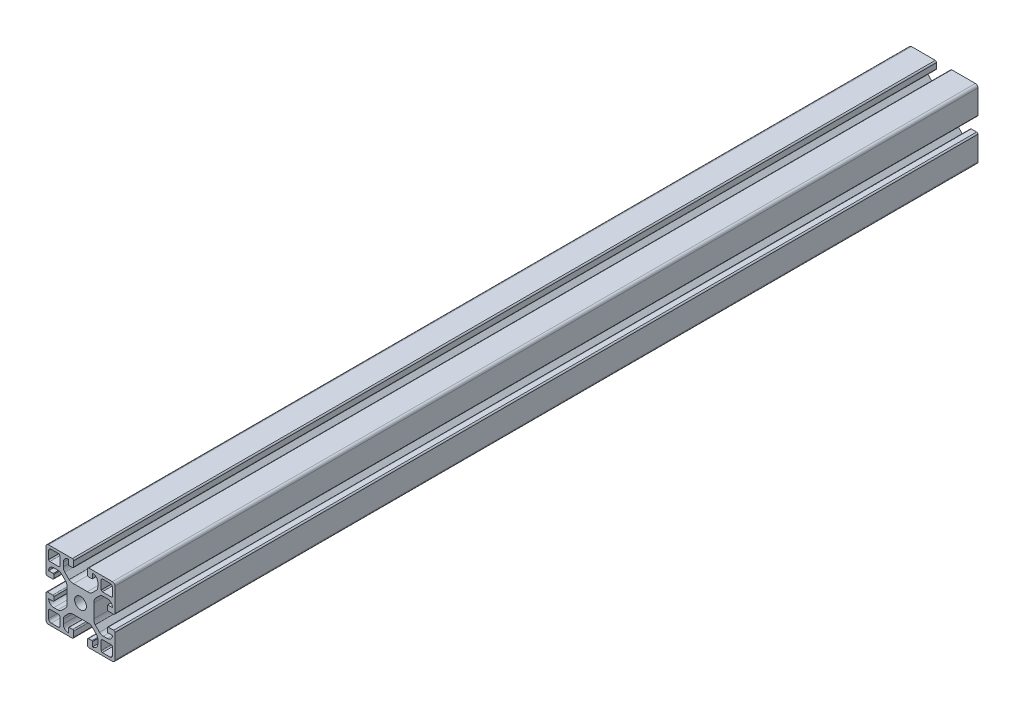
SolidWorks part; units mm, degrees
ref_plane "Alzado" through (0, 0, 0) normal (0, 0, 1) x (1, 0, 0)
ref_plane "Planta" through (0, 0, 0) normal (0, 1, 0) x (1, 0, 0)
ref_plane "Vista lateral" through (0, 0, 0) normal (1, 0, 0) x (0, 0, -1)
sketch "Croquis1" plane through (0, 0, 0) normal (0, 0, 1) x (1, 0, 0)
  line L9 (0, 18.5) -> (0, 4.7232)
  line L10 (0.7765, 4) -> (3.8765, 4)
  line L12 (12.25, -4.7232) -> (12.25, 4.7232)
  line L14 (4.5, 4.5616) -> (4.5, 6.6755)
  line L15 (4.2267, 7) -> (1.5, 7)
  line L17 (9.0164, 9.1211) -> (11.5076, 6.6299)
  line L18 (6.9331, 10) -> (4.5, 10)
  line L19 (40, -18.5) -> (40, -4.7232)
  line L20 (5.7166, 12) -> (7.3817, 12)
  line L21 (5.7166, 12) -> (2.23, 12)
  line L22 (1.5, 12.6183) -> (1.5, 17)
  line L23 (24.7232, 7.75) -> (15.2768, 7.75)
  line L24 (10.8789, 10.9836) -> (13.3701, 8.4924)
  line L25 (10, 13.0669) -> (10, 15.5)
  line L26 (13, 15.7733) -> (13, 18.5)
  line L27 (15.4384, 15.5) -> (13.3245, 15.5)
  line L28 (16, 19.2235) -> (16, 16.1235)
  line L29 (1.3293, 20) -> (15.2768, 20)
  line L30 (8, 14.2834) -> (8, 12.6183)
  line L31 (8, 14.2834) -> (8, 17.77)
  line L32 (7.3817, 18.5) -> (3, 18.5)
  line L33 (32.6183, 18.5) -> (37, 18.5)
  line L34 (32, 14.2834) -> (32, 17.77)
  line L35 (32, 14.2834) -> (32, 12.6183)
  line L36 (38.6707, 20) -> (24.7232, 20)
  line L37 (24, 19.2235) -> (24, 16.1235)
  line L38 (24.5616, 15.5) -> (26.6755, 15.5)
  line L39 (27, 15.7733) -> (27, 18.5)
  line L40 (30, 13.0669) -> (30, 15.5)
  line L41 (29.1211, 10.9836) -> (26.6299, 8.4924)
  line L42 (38.5, 12.6183) -> (38.5, 17)
  line L43 (34.2834, 12) -> (37.77, 12)
  line L44 (34.2834, 12) -> (32.6183, 12)
  line L45 (33.0669, 10) -> (35.5, 10)
  line L46 (30.9836, 9.1211) -> (28.4924, 6.6299)
  line L47 (35.7733, 7) -> (38.5, 7)
  line L48 (35.5, 4.5616) -> (35.5, 6.6755)
  line L49 (27.75, -4.7232) -> (27.75, 4.7232)
  line L51 (39.2235, 4) -> (36.1235, 4)
  line L52 (40, 18.5) -> (40, 4.7232)
  line L53 (39.2235, -4) -> (36.1235, -4)
  line L54 (35.5, -4.5616) -> (35.5, -6.6755)
  line L55 (35.7733, -7) -> (38.5, -7)
  line L56 (30.9836, -9.1211) -> (28.4924, -6.6299)
  line L57 (33.0669, -10) -> (35.5, -10)
  line L58 (34.2834, -12) -> (32.6183, -12)
  line L59 (34.2834, -12) -> (37.77, -12)
  line L60 (38.5, -12.6183) -> (38.5, -17)
  line L61 (29.1211, -10.9836) -> (26.6299, -8.4924)
  line L62 (30, -13.0669) -> (30, -15.5)
  line L63 (27, -15.7733) -> (27, -18.5)
  line L64 (24.5616, -15.5) -> (26.6755, -15.5)
  line L65 (24, -19.2235) -> (24, -16.1235)
  line L66 (38.6707, -20) -> (24.7232, -20)
  line L67 (32, -14.2834) -> (32, -12.6183)
  line L68 (32, -14.2834) -> (32, -17.77)
  line L69 (32.6183, -18.5) -> (37, -18.5)
  line L70 (7.3817, -18.5) -> (3, -18.5)
  line L71 (8, -14.2834) -> (8, -17.77)
  line L72 (8, -14.2834) -> (8, -12.6183)
  line L73 (1.3293, -20) -> (15.2768, -20)
  line L74 (16, -19.2235) -> (16, -16.1235)
  line L75 (15.4384, -15.5) -> (13.3245, -15.5)
  line L76 (13, -15.7733) -> (13, -18.5)
  line L77 (10, -13.0669) -> (10, -15.5)
  line L78 (10.8789, -10.9836) -> (13.3701, -8.4924)
  line L79 (24.7232, -7.75) -> (15.2768, -7.75)
  line L80 (1.5, -12.6183) -> (1.5, -17)
  line L81 (5.7166, -12) -> (2.23, -12)
  line L82 (5.7166, -12) -> (7.3817, -12)
  line L83 (6.9331, -10) -> (4.5, -10)
  line L84 (9.0164, -9.1211) -> (11.5076, -6.6299)
  line L85 (4.2267, -7) -> (1.5, -7)
  line L86 (4.5, -4.5616) -> (4.5, -6.6755)
  line L87 (0.7765, -4) -> (3.8765, -4)
  line L88 (0, -18.5) -> (0, -4.7232)
  arc A0 (4.5, 10) -> (1.5, 7) centre (4.5, 7) ccw
  arc A1 (10, 15.5) -> (13, 18.5) centre (13, 15.5) cw
  arc A2 (0, 18.5) -> (1.5, 20) centre (1.5, 18.5) cw
  arc A3 (1.5, 17) -> (3, 18.5) centre (3, 17) cw
  circle A4 centre (20, 0) radius 3.4
  arc A5 (38.5, 17) -> (37, 18.5) centre (37, 17) ccw
  arc A6 (40, 18.5) -> (38.5, 20) centre (38.5, 18.5) ccw
  arc A7 (30, 15.5) -> (27, 18.5) centre (27, 15.5) ccw
  arc A8 (35.5, 10) -> (38.5, 7) centre (35.5, 7) cw
  arc A9 (35.5, -10) -> (38.5, -7) centre (35.5, -7) ccw
  arc A10 (30, -15.5) -> (27, -18.5) centre (27, -15.5) cw
  arc A11 (40, -18.5) -> (38.5, -20) centre (38.5, -18.5) cw
  arc A12 (38.5, -17) -> (37, -18.5) centre (37, -17) cw
  arc A13 (1.5, -17) -> (3, -18.5) centre (3, -17) ccw
  arc A14 (0, -18.5) -> (1.5, -20) centre (1.5, -18.5) ccw
  arc A15 (10, -15.5) -> (13, -18.5) centre (13, -15.5) ccw
  arc A16 (4.5, -10) -> (1.5, -7) centre (4.5, -7) cw
  spline S0 degree 2 poles (6.7957, 10) (8.0801, 10.025) (9.0164, 9.1211) knots 0 0 0 1 1 1
  spline S1 degree 2 poles (11.5076, 6.6299) (12.3742, 5.4854) (12.25, 4) knots 0 0 0 1 1 1
  spline S2 degree 2 poles (0, 4.7232) (0.1682, 4.1542) (0.7765, 4) knots 0 0 0 1 1 1
  spline S3 degree 2 poles (3.8765, 4) (4.593, 4.0978) (4.5, 4.8884) knots 0 0 0 1 1 1
  spline S4 degree 2 poles (4.2267, 7) (4.4426, 6.908) (4.5, 6.6755) knots 0 0 0 1 1 1
  spline S5 degree 2 poles (13.3701, 8.4924) (14.5146, 7.6258) (16, 7.75) knots 0 0 0 1 1 1
  spline S6 degree 2 poles (10, 13.2043) (9.975, 11.9199) (10.8789, 10.9836) knots 0 0 0 1 1 1
  spline S7 degree 2 poles (13, 15.7733) (13.092, 15.5574) (13.3245, 15.5) knots 0 0 0 1 1 1
  spline S8 degree 2 poles (16, 16.1235) (15.9022, 15.407) (15.1116, 15.5) knots 0 0 0 1 1 1
  spline S9 degree 2 poles (15.2768, 20) (15.8458, 19.8318) (16, 19.2235) knots 0 0 0 1 1 1
  spline S10 degree 2 poles (1.5, 12.6183) (1.6133, 12.0451) (2.23, 12) knots 0 0 0 1 1 1
  spline S11 degree 2 poles (7.3817, 18.5) (7.9549, 18.3867) (8, 17.77) knots 0 0 0 1 1 1
  spline S12 degree 2 poles (7.3817, 12) (7.9101, 12.0752) (8, 12.6183) knots 0 0 0 1 1 1
  spline S13 degree 2 poles (32.6183, 12) (32.0899, 12.0752) (32, 12.6183) knots 0 0 0 1 1 1
  spline S14 degree 2 poles (32.6183, 18.5) (32.0451, 18.3867) (32, 17.77) knots 0 0 0 1 1 1
  spline S15 degree 2 poles (38.5, 12.6183) (38.3867, 12.0451) (37.77, 12) knots 0 0 0 1 1 1
  spline S16 degree 2 poles (24.7232, 20) (24.1542, 19.8318) (24, 19.2235) knots 0 0 0 1 1 1
  spline S17 degree 2 poles (24, 16.1235) (24.0978, 15.407) (24.8884, 15.5) knots 0 0 0 1 1 1
  spline S18 degree 2 poles (27, 15.7733) (26.908, 15.5574) (26.6755, 15.5) knots 0 0 0 1 1 1
  spline S19 degree 2 poles (30, 13.2043) (30.025, 11.9199) (29.1211, 10.9836) knots 0 0 0 1 1 1
  spline S20 degree 2 poles (26.6299, 8.4924) (25.4854, 7.6258) (24, 7.75) knots 0 0 0 1 1 1
  spline S21 degree 2 poles (35.7733, 7) (35.5574, 6.908) (35.5, 6.6755) knots 0 0 0 1 1 1
  spline S22 degree 2 poles (36.1235, 4) (35.407, 4.0978) (35.5, 4.8884) knots 0 0 0 1 1 1
  spline S23 degree 2 poles (40, 4.7232) (39.8318, 4.1542) (39.2235, 4) knots 0 0 0 1 1 1
  spline S24 degree 2 poles (28.4924, 6.6299) (27.6258, 5.4854) (27.75, 4) knots 0 0 0 1 1 1
  spline S25 degree 2 poles (33.2043, 10) (31.9199, 10.025) (30.9836, 9.1211) knots 0 0 0 1 1 1
  spline S26 degree 2 poles (33.2043, -10) (31.9199, -10.025) (30.9836, -9.1211) knots 0 0 0 1 1 1
  spline S27 degree 2 poles (28.4924, -6.6299) (27.6258, -5.4854) (27.75, -4) knots 0 0 0 1 1 1
  spline S28 degree 2 poles (40, -4.7232) (39.8318, -4.1542) (39.2235, -4) knots 0 0 0 1 1 1
  spline S29 degree 2 poles (36.1235, -4) (35.407, -4.0978) (35.5, -4.8884) knots 0 0 0 1 1 1
  spline S30 degree 2 poles (35.7733, -7) (35.5574, -6.908) (35.5, -6.6755) knots 0 0 0 1 1 1
  spline S31 degree 2 poles (26.6299, -8.4924) (25.4854, -7.6258) (24, -7.75) knots 0 0 0 1 1 1
  spline S32 degree 2 poles (30, -13.2043) (30.025, -11.9199) (29.1211, -10.9836) knots 0 0 0 1 1 1
  spline S33 degree 2 poles (27, -15.7733) (26.908, -15.5574) (26.6755, -15.5) knots 0 0 0 1 1 1
  spline S34 degree 2 poles (24, -16.1235) (24.0978, -15.407) (24.8884, -15.5) knots 0 0 0 1 1 1
  spline S35 degree 2 poles (24.7232, -20) (24.1542, -19.8318) (24, -19.2235) knots 0 0 0 1 1 1
  spline S36 degree 2 poles (38.5, -12.6183) (38.3867, -12.0451) (37.77, -12) knots 0 0 0 1 1 1
  spline S37 degree 2 poles (32.6183, -18.5) (32.0451, -18.3867) (32, -17.77) knots 0 0 0 1 1 1
  spline S38 degree 2 poles (32.6183, -12) (32.0899, -12.0752) (32, -12.6183) knots 0 0 0 1 1 1
  spline S39 degree 2 poles (7.3817, -12) (7.9101, -12.0752) (8, -12.6183) knots 0 0 0 1 1 1
  spline S40 degree 2 poles (7.3817, -18.5) (7.9549, -18.3867) (8, -17.77) knots 0 0 0 1 1 1
  spline S41 degree 2 poles (1.5, -12.6183) (1.6133, -12.0451) (2.23, -12) knots 0 0 0 1 1 1
  spline S42 degree 2 poles (15.2768, -20) (15.8458, -19.8318) (16, -19.2235) knots 0 0 0 1 1 1
  spline S43 degree 2 poles (16, -16.1235) (15.9022, -15.407) (15.1116, -15.5) knots 0 0 0 1 1 1
  spline S44 degree 2 poles (13, -15.7733) (13.092, -15.5574) (13.3245, -15.5) knots 0 0 0 1 1 1
  spline S45 degree 2 poles (10, -13.2043) (9.975, -11.9199) (10.8789, -10.9836) knots 0 0 0 1 1 1
  spline S46 degree 2 poles (13.3701, -8.4924) (14.5146, -7.6258) (16, -7.75) knots 0 0 0 1 1 1
  spline S47 degree 2 poles (4.2267, -7) (4.4426, -6.908) (4.5, -6.6755) knots 0 0 0 1 1 1
  spline S48 degree 2 poles (3.8765, -4) (4.593, -4.0978) (4.5, -4.8884) knots 0 0 0 1 1 1
  spline S49 degree 2 poles (0, -4.7232) (0.1682, -4.1542) (0.7765, -4) knots 0 0 0 1 1 1
  spline S50 degree 2 poles (11.5076, -6.6299) (12.3742, -5.4854) (12.25, -4) knots 0 0 0 1 1 1
  spline S51 degree 2 poles (6.7957, -10) (8.0801, -10.025) (9.0164, -9.1211) knots 0 0 0 1 1 1
extrude "Saliente-Extruir1" add sketch "Croquis1" along normal blind 500 contours S51 L83 A16 L85 S47 L86 S48 L87 S49 L88 A14 L73 S42 L74 S43 L75 S44 L76 A15 L77 S45 L78 S46 L79 S31 L61 S32 L62 A10 L63 S33 L64 S34 L65 S35 L66 A11 L19 S28 L53 S29 L54 S30
